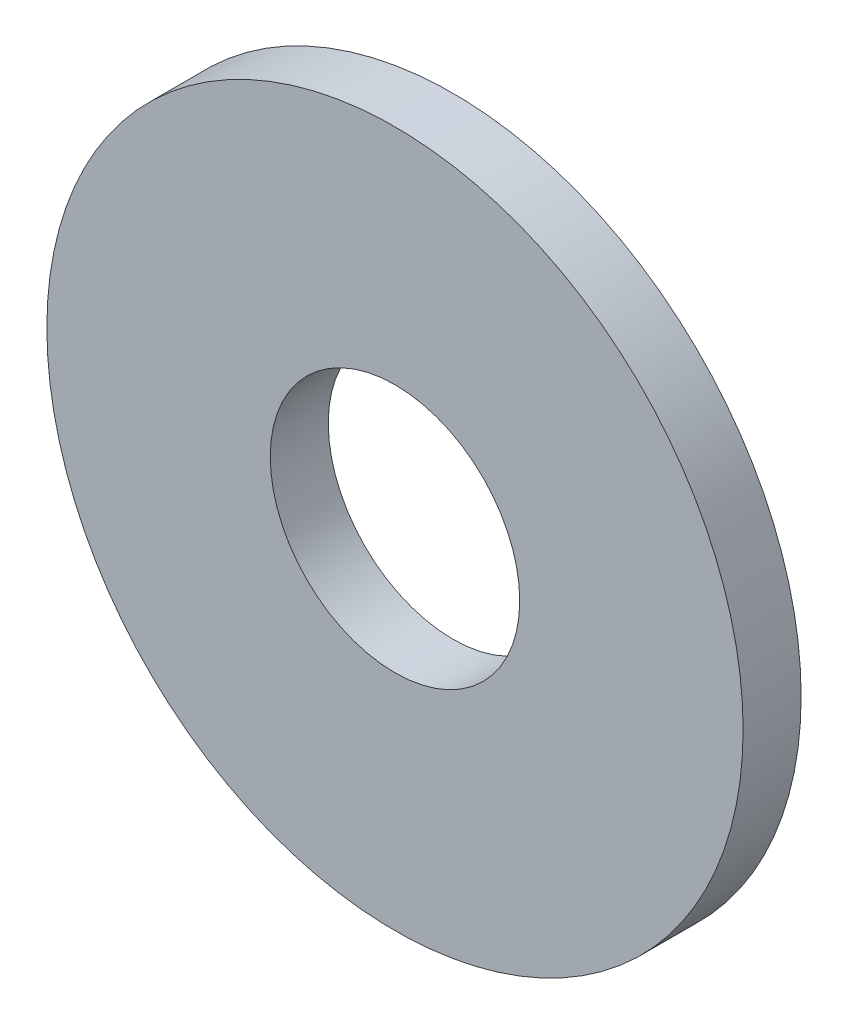
SolidWorks part; units mm, degrees
ref_plane "Front" through (0, 0, 0) normal (0, 0, 1) x (1, 0, 0)
ref_plane "Top" through (0, 0, 0) normal (0, 1, 0) x (1, 0, 0)
ref_plane "Right" through (0, 0, 0) normal (1, 0, 0) x (0, 0, -1)
sketch "Sketch1" plane through (0, 0, 0) normal (0, 0, 1) x (1, 0, 0)
  circle A0 centre (0, 0) radius 2.15
  circle A1 centre (0, 0) radius 6
  dimension "d1" = 4.3
  dimension "d2" = 12
extrude "Base-Extrude" add sketch "Sketch1" against normal blind 1
